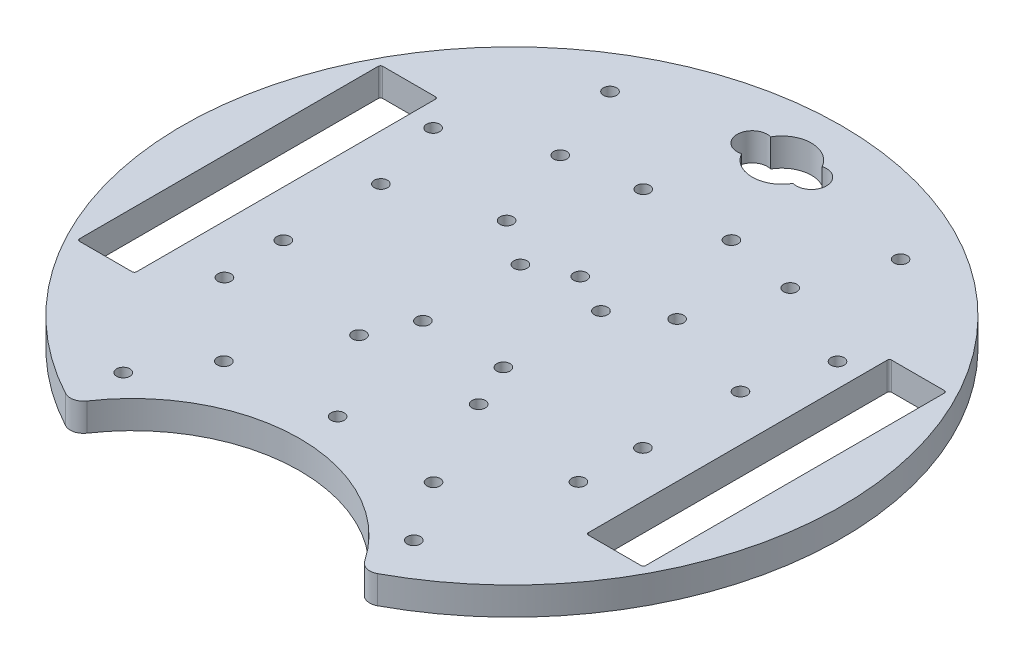
SolidWorks part; units mm, degrees
ref_plane "Front Plane" through (0, 0, 0) normal (0, 0, 1) x (1, 0, 0)
ref_plane "Top Plane" through (0, 0, 0) normal (0, 1, 0) x (1, 0, 0)
ref_plane "Right Plane" through (0, 0, 0) normal (1, 0, 0) x (0, 0, -1)
sketch "Sketch1" plane through (0, 0, 0) normal (0, 1, 0) x (1, 0, 0)
  line L0 (0, 0) -> (-51.5062, -59.2511) construction
  line L1 (0, 86.2583) -> (0, -96.8543) construction
  line L2 (-26.1633, 37.1696) -> (-32.2721, 24.2954) construction
  line L3 (-32.9956, -67.352) -> (0, -86.402) construction
  line L4 (32.9956, -67.352) -> (0, -86.402) construction
  line L5 (0, 0) -> (-13.6167, -50.8184) construction
  line L6 (-33.3347, -42.5389) -> (-41.6896, -52.1501) construction
  line L7 (-32.2721, 24.2954) -> (-46.0115, 28.0759) construction
  line L8 (-83.3992, 0) -> (107.0959, 0) construction
  line L9 (51.4101, -34) -> (51.4101, 34)
  line L10 (-63.9101, -34.5) -> (-51.9101, -34.5)
  line L11 (-64.4101, -34) -> (-64.4101, 34)
  line L12 (-63.9101, 34.5) -> (-51.9101, 34.5)
  line L13 (-51.4101, -34) -> (-51.4101, 34)
  line L14 (63.9101, 34.5) -> (51.9101, 34.5)
  line L15 (64.4101, -34) -> (64.4101, 34)
  line L16 (63.9101, -34.5) -> (51.9101, -34.5)
  line L17 (0, 0) -> (13.6167, -50.8184) construction
  line L18 (-33.3347, -42.5389) -> (-37.4856, -38.9306) construction
  line L19 (0, 0) -> (-95.645, -6.6882) construction
  line L20 (-37.4856, -38.9306) -> (-45.4633, -48.1079) construction
  line L21 (-42.5389, 33.3347) -> (-51.7162, 41.3124) construction
  line L22 (33.3347, -42.5389) -> (41.6896, -52.1501) construction
  line L23 (37.4856, -38.9306) -> (45.4633, -48.1079) construction
  line L24 (-38.9306, 37.4856) -> (-42.5389, 33.3347) construction
  line L25 (-38.9306, 37.4856) -> (-48.5418, 45.8405) construction
  line L26 (33.3347, -42.5389) -> (37.4856, -38.9306) construction
  line L27 (38.9306, 37.4856) -> (42.5389, 33.3347) construction
  line L28 (42.5389, 33.3347) -> (51.7162, 41.3124) construction
  line L29 (-18.4555, -45.8919) -> (-23.0541, -33.9225) construction
  line L30 (-23.0541, -33.9225) -> (-17.92, -31.9499) construction
  line L31 (38.9306, 37.4856) -> (48.5418, 45.8405) construction
  line L32 (-57.9101, -34.5) -> (-57.9101, 19.5819) construction
  line L35 (-13.6167, -50.8184) -> (-25.1096, -20.9046) construction
  line L37 (-13.3214, -43.9193) -> (-17.92, -31.9499) construction
  line L38 (13.6167, -50.8184) -> (24.3327, -22.8079) construction
  line L39 (18.4555, -45.8919) -> (23.0541, -33.9225) construction
  line L40 (23.0541, -33.9225) -> (17.92, -31.9499) construction
  line L41 (13.3214, -43.9193) -> (17.92, -31.9499) construction
  line L42 (-58.5537, 0) -> (91.2411, 0) construction
  line L46 (0, 34.6626) -> (0, -51.647) construction
  line L47 (-37.1849, 0) -> (48.113, 0) construction
  line L48 (0, 49.2959) -> (0, -33.0158) construction
  arc A0 (35.4973, -66.0677) -> (-35.4973, -66.0677) centre (0, 0) ccw
  arc A1 (31.59, -65.1022) -> (-31.59, -65.1022) centre (0, -86.402) ccw
  circle A2 centre (0, 0) radius 74 construction
  circle A3 centre (-13.6089, -21.1831) radius 1.5
  circle A4 centre (27.6453, -18.6148) radius 14.218 construction
  arc A5 (40.0385, -63.4186) -> (41.6896, -52.1501) centre (36.0347, -57.0767) ccw construction
  arc A6 (57.2141, -48.4928) -> (45.4633, -48.1079) centre (51.4912, -43.6452) cw construction
  circle A7 centre (27.6453, -18.6148) radius 12.095 construction
  circle A8 centre (-46.0115, 28.0759) radius 1.5
  circle A9 centre (13.6089, -21.1831) radius 1.5
  circle A10 centre (23.8525, -41.6946) radius 1.5
  arc A11 (-57.2141, -48.4928) -> (-45.4633, -48.1079) centre (-51.4912, -43.6452) ccw construction
  arc A12 (-40.0385, -63.4186) -> (-41.6896, -52.1501) centre (-36.0347, -57.0767) cw construction
  arc A13 (-5.2684, -48.6449) -> (-13.3214, -43.9193) centre (-6.3241, -41.2196) cw construction
  arc A14 (-21.2728, -54.7938) -> (-18.4555, -45.8919) centre (-25.4604, -48.5717) ccw construction
  circle A15 centre (-26.2497, -27.6477) radius 12.095 construction
  circle A16 centre (-26.2497, -27.6477) radius 14.25 construction
  arc A17 (21.2728, -54.7938) -> (18.4555, -45.8919) centre (25.4604, -48.5717) cw construction
  arc A18 (5.2684, -48.6449) -> (13.3214, -43.9193) centre (6.3241, -41.2196) ccw construction
  circle A19 centre (-40.9101, 11.1) radius 1.5
  circle A20 centre (-40.9101, -11.1) radius 1.5
  circle A21 centre (-9.1601, -11.1) radius 1.5
  circle A22 centre (-9.1601, 11.1) radius 1.5
  circle A23 centre (9.1601, 11.1) radius 1.5
  circle A24 centre (9.1601, -11.1) radius 1.5
  circle A25 centre (40.9101, -11.1) radius 1.5
  circle A26 centre (40.9101, 11.1) radius 1.5
  circle A27 centre (-23.8525, -41.6946) radius 1.5
  circle A28 centre (19.3979, 18.1866) radius 1.5
  circle A29 centre (0, 29.7936) radius 12.095 construction
  circle A30 centre (0, -25.4092) radius 12.095 construction
  circle A31 centre (-40.2774, -25.1402) radius 1.5
  circle A32 centre (40.2774, -25.1402) radius 1.5
  circle A33 centre (6.731, 61.4226) radius 1.143
  circle A34 centre (-6.731, 61.4226) radius 1.143
  arc A35 (-5.8539, 64.7449) -> (5.8576, 64.7385) centre (0, 61.4226) cw
  arc A36 (5.8576, 64.7385) -> (5.8576, 58.1067) centre (6.731, 61.4226) cw
  arc A37 (-5.8539, 58.1002) -> (-5.8539, 64.7449) centre (-6.731, 61.4226) cw
  arc A38 (5.8576, 58.1067) -> (-5.8539, 58.1002) centre (0, 61.4226) cw
  circle A39 centre (26.2497, -27.6477) radius 14.25 construction
  circle A42 centre (32.2721, 24.2954) radius 14.25 construction
  circle A43 centre (-32.2721, 24.2954) radius 12.095 construction
  circle A44 centre (26.1633, 37.1696) radius 1.5
  circle A45 centre (32.2721, 24.2954) radius 12.095 construction
  circle A46 centre (-27.6453, -18.6148) radius 12.095 construction
  circle A47 centre (26.2497, -27.6477) radius 12.095 construction
  circle A48 centre (46.0115, 28.0759) radius 1.5
  circle A49 centre (-20.0544, 50.0438) radius 12.095 construction
  circle A50 centre (10.0272, 39.9187) radius 1.5
  arc A51 (-35.4973, -66.0677) -> (-31.59, -65.1022) centre (-34.0774, -63.425) ccw
  arc A52 (35.4973, -66.0677) -> (31.59, -65.1022) centre (34.0774, -63.425) cw
  circle A53 centre (0, -39.6592) radius 1.5
  circle A54 centre (-32.2721, 24.2954) radius 14.25 construction
  circle A55 centre (-10.0272, 39.9187) radius 1.5
  circle A56 centre (20.0544, 50.0438) radius 14.25 construction
  circle A57 centre (20.0544, 50.0438) radius 12.095 construction
  circle A58 centre (0, 29.7936) radius 14.25 construction
  circle A59 centre (-33.0597, -55.3832) radius 1.5
  circle A60 centre (-33.0597, 55.3832) radius 1.5
  circle A61 centre (33.0597, -55.3832) radius 1.5
  circle A62 centre (0, 15.5436) radius 1.5
  circle A63 centre (-26.1633, 37.1696) radius 1.5
  circle A64 centre (0, 0) radius 64.5 construction
  circle A65 centre (-19.3979, 18.1866) radius 1.5
  circle A66 centre (-20.0544, 50.0438) radius 14.25 construction
  circle A67 centre (33.0597, 55.3832) radius 1.5
  arc A68 (-48.475, 57.2291) -> (-48.5418, 45.8405) centre (-43.6275, 51.5062) ccw construction
  arc A69 (-63.4062, 40.0581) -> (-51.7162, 41.3124) centre (-57.0643, 36.0543) cw construction
  arc A70 (63.4062, 40.0581) -> (51.7162, 41.3124) centre (57.0643, 36.0543) ccw construction
  arc A71 (48.475, 57.2291) -> (48.5418, 45.8405) centre (43.6275, 51.5062) cw construction
  arc A72 (-64.4101, -34) -> (-63.9101, -34.5) centre (-63.9101, -34) ccw
  arc A73 (-51.4101, -34) -> (-51.9101, -34.5) centre (-51.9101, -34) cw
  circle A74 centre (-27.6453, -18.6148) radius 14.218 construction
  arc A75 (-51.4101, 34) -> (-51.9101, 34.5) centre (-51.9101, 34) ccw
  arc A76 (-64.4101, 34) -> (-63.9101, 34.5) centre (-63.9101, 34) cw
  arc A77 (64.4101, 34) -> (63.9101, 34.5) centre (63.9101, 34) ccw
  circle A78 centre (0, -25.4092) radius 14.25 construction
  arc A79 (51.4101, 34) -> (51.9101, 34.5) centre (51.9101, 34) cw
  arc A80 (51.4101, -34) -> (51.9101, -34.5) centre (51.9101, -34) ccw
  arc A81 (64.4101, -34) -> (63.9101, -34.5) centre (63.9101, -34) cw
  point P14 (-62.6039, 0)
  point P23 (62.6039, 0)
  point P35 (-31.5178, -45.012)
  point P40 (-46.7211, -26.9744)
  point P45 (-23.8153, 50.3782)
  point P48 (0, -25.4092)
  point P84 (-20.4871, -32.9362)
  point P154 (0, 58.1002)
  dimension "D1" = 150
  dimension "D2" = 76.2
  dimension "D10" = 148
  dimension "D13" = 3
  dimension "D14" = 3
  dimension "D22" = 2.286
  dimension "D20" = 3
  dimension "D11" = 24.19
  dimension "D12" = 28.436
  dimension "D24" = 28.5
  dimension "D21" = 24.19
  dimension "D25" = 28.5
  dimension "D26" = 28.5
  dimension "D29" = 28.5
  dimension "D8" = 28.5
  dimension "D16" = 6
  dimension "D3" = 120
  dimension "D9" = 30
  dimension "D6" = 12.8224
  dimension "D17" = 22.2
  dimension "D19" = 22.2
  dimension "D15" = 10.5
  dimension "D18" = 31.75
  dimension "D23" = 13.462
  dimension "D31" = 100
  dimension "D27" = 45
  dimension "D28" = 12.735
  dimension "D4" = 13
  dimension "D30" = 170
extrude "Boss-Extrude2" add sketch "Sketch1" along normal blind 6.35
fillet "Fillet1" [suppressed] radius 2
equation "\"D10@Sketch1\"=150-2"
